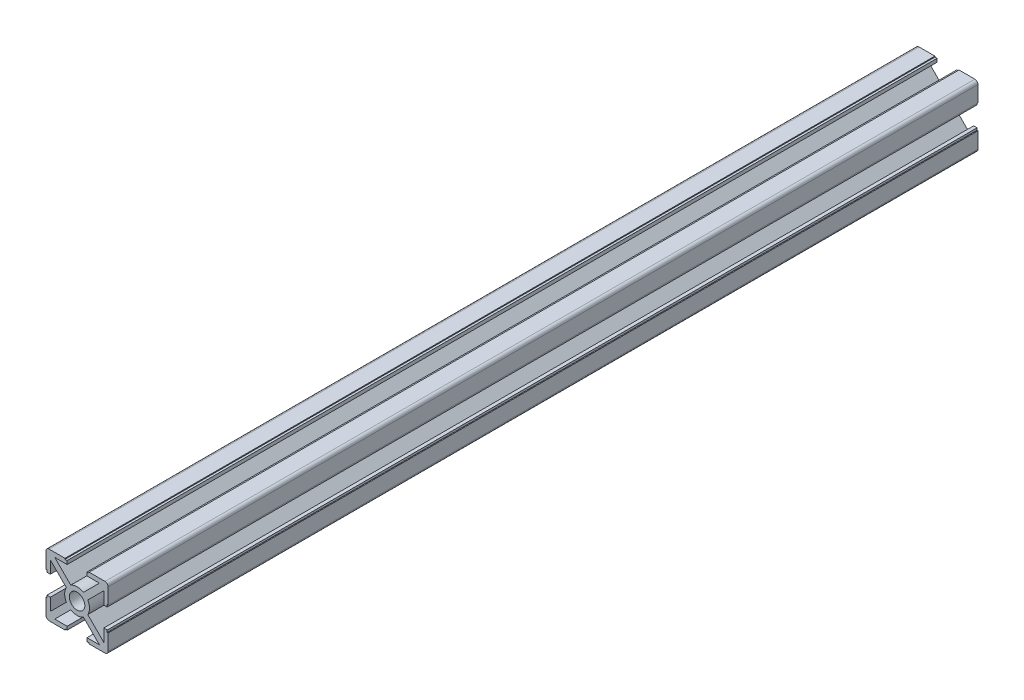
SolidWorks part; units mm, degrees
material "1060 Alloy"
ref_plane "Ön Düzlem" through (0, 0, 0) normal (0, 0, 1) x (1, 0, 0)
ref_plane "Üst Düzlem" through (0, 0, 0) normal (0, 1, 0) x (1, 0, 0)
ref_plane "Sağ Düzlem" through (0, 0, 0) normal (1, 0, 0) x (0, 0, -1)
sketch "Sketch1" plane through (0, 0, 0) normal (0, 0, 1) x (1, 0, 0)
  line L0 (-9.7071, -3.2) -> (-8.6, -3.2)
  line L2 (-10, -3.8775) -> (-10, -9)
  line L3 (-9, -10) -> (-3.8775, -10)
  line L5 (-10, -3.8775) -> (-9.7071, -3.8775)
  line L6 (-10, -10) -> (-9.7071, -9.7071) construction
  line L9 (-3.2, -8.6) -> (-7.1858, -8.6)
  line L10 (-8.6, -3.2) -> (-8.6, -7.1858)
  line L13 (-7.1858, -8.6) -> (-2.0315, -3.4457)
  line L14 (-8.6, -7.1858) -> (-3.4457, -2.0315)
  line L15 (-10.7071, -9.2929) -> (9.2929, 10.7071) construction
  line L16 (-9.2929, -10.7071) -> (10.7071, 9.2929) construction
  line L18 (-10, -10) -> (10, 10) construction
  line L19 (-2.5, 0) -> (-9.7071, 0) construction
  line L20 (0, -2.5) -> (0, -6.9362) construction
  line L21 (-3.2, -8.6) -> (-3.2, -9.7071)
  line L23 (-9.7071, -3.8775) -> (-9.7071, -3.2)
  line L24 (-3.2, -9.7071) -> (-3.8775, -9.7071)
  line L25 (-3.8775, -9.7071) -> (-3.8775, -10)
  line L28 (10, -10) -> (9.7071, -9.7071) construction
  line L30 (3.8775, -9.7071) -> (3.8775, -10)
  line L31 (3.2, -9.7071) -> (3.8775, -9.7071)
  line L32 (9.7071, -3.8775) -> (9.7071, -3.2)
  line L33 (3.2, -8.6) -> (3.2, -9.7071)
  line L34 (8.6, -7.1858) -> (3.4457, -2.0315)
  line L35 (7.1858, -8.6) -> (2.0315, -3.4457)
  line L36 (8.6, -3.2) -> (8.6, -7.1858)
  line L37 (3.2, -8.6) -> (7.1858, -8.6)
  line L38 (10, -3.8775) -> (9.7071, -3.8775)
  line L39 (9, -10) -> (3.8775, -10)
  line L40 (10, -3.8775) -> (10, -9)
  line L41 (9.7071, -3.2) -> (8.6, -3.2)
  line L42 (10, 10) -> (9.7071, 9.7071) construction
  line L43 (0, 2.5) -> (0, 6.9362) construction
  line L44 (-10, 10) -> (-9.7071, 9.7071) construction
  line L45 (9.7071, 3.2) -> (8.6, 3.2)
  line L46 (10, 3.8775) -> (10, 9)
  line L47 (9, 10) -> (3.8775, 10)
  line L48 (10, 3.8775) -> (9.7071, 3.8775)
  line L49 (3.2, 8.6) -> (7.1858, 8.6)
  line L50 (8.6, 3.2) -> (8.6, 7.1858)
  line L51 (7.1858, 8.6) -> (2.0315, 3.4457)
  line L52 (8.6, 7.1858) -> (3.4457, 2.0315)
  line L53 (3.2, 8.6) -> (3.2, 9.7071)
  line L54 (9.7071, 3.8775) -> (9.7071, 3.2)
  line L55 (3.2, 9.7071) -> (3.8775, 9.7071)
  line L56 (3.8775, 9.7071) -> (3.8775, 10)
  line L57 (-3.8775, 9.7071) -> (-3.8775, 10)
  line L58 (-3.2, 9.7071) -> (-3.8775, 9.7071)
  line L59 (-9.7071, 3.8775) -> (-9.7071, 3.2)
  line L60 (-3.2, 8.6) -> (-3.2, 9.7071)
  line L61 (-8.6, 7.1858) -> (-3.4457, 2.0315)
  line L62 (-7.1858, 8.6) -> (-2.0315, 3.4457)
  line L63 (-8.6, 3.2) -> (-8.6, 7.1858)
  line L64 (-3.2, 8.6) -> (-7.1858, 8.6)
  line L65 (-10, 3.8775) -> (-9.7071, 3.8775)
  line L66 (-9, 10) -> (-3.8775, 10)
  line L67 (-10, 3.8775) -> (-10, 9)
  line L68 (-9.7071, 3.2) -> (-8.6, 3.2)
  arc A2 (-10, -9) -> (-9, -10) centre (-9, -9) ccw
  arc A3 (-2.0315, -3.4457) -> (2.0315, -3.4457) centre (0, 0) ccw
  arc A4 (-3.4457, 2.0315) -> (-3.4457, -2.0315) centre (0, 0) ccw
  circle A5 centre (0, 0) radius 2.5
  arc A6 (3.4457, 2.0315) -> (3.4457, -2.0315) centre (0, 0) cw
  arc A7 (10, -9) -> (9, -10) centre (9, -9) cw
  arc A8 (10, 9) -> (9, 10) centre (9, 9) ccw
  arc A9 (-2.0315, 3.4457) -> (2.0315, 3.4457) centre (0, 0) cw
  arc A10 (-10, 9) -> (-9, 10) centre (-9, 9) cw
  dimension "D10" = 1
  dimension "D5" = 1.4
  dimension "D6" = 1.4
  dimension "D7" = 3.2
  dimension "D11" = 3.2
  dimension "D8" = 1
  dimension "D9" = 1
extrude "Boss-Extrude1" add sketch "Sketch1" along normal blind 280
